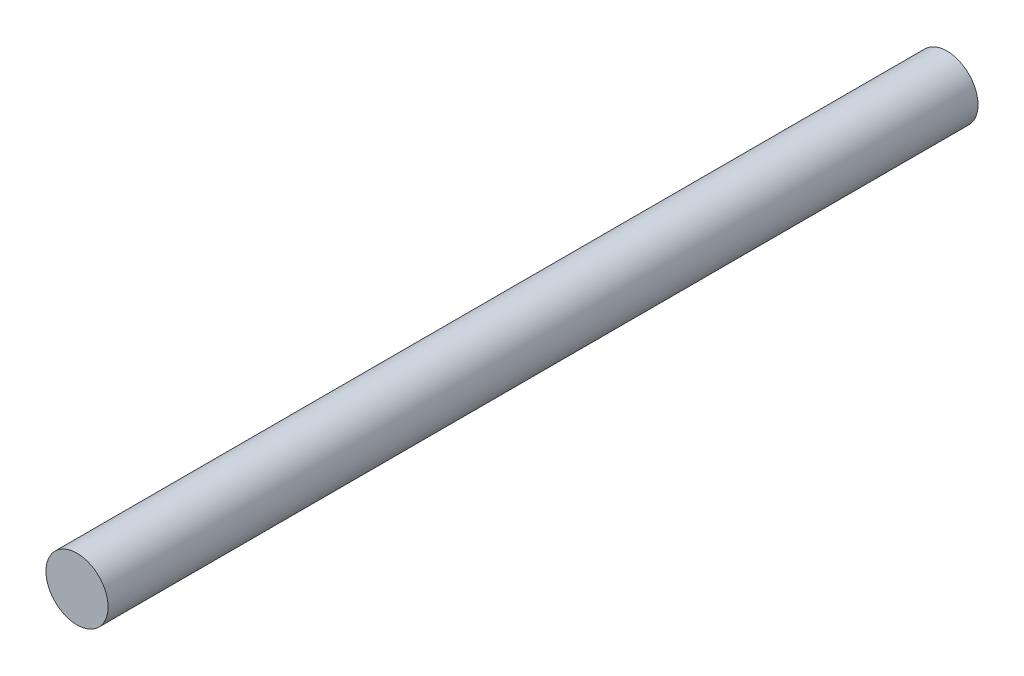
SolidWorks part; units mm, degrees
ref_plane "Front Plane" through (0, 0, 0) normal (0, 0, 1) x (1, 0, 0)
ref_plane "Top Plane" through (0, 0, 0) normal (0, 1, 0) x (1, 0, 0)
ref_plane "Right Plane" through (0, 0, 0) normal (1, 0, 0) x (0, 0, -1)
sketch "Sketch1" plane through (0, 0, 0) normal (0, 0, 1) x (1, 0, 0)
  circle A0 centre (0, 0) radius 12.7
  dimension "D1" = 25.4
extrude "Boss-Extrude1" add sketch "Sketch1" along normal blind 355.6
